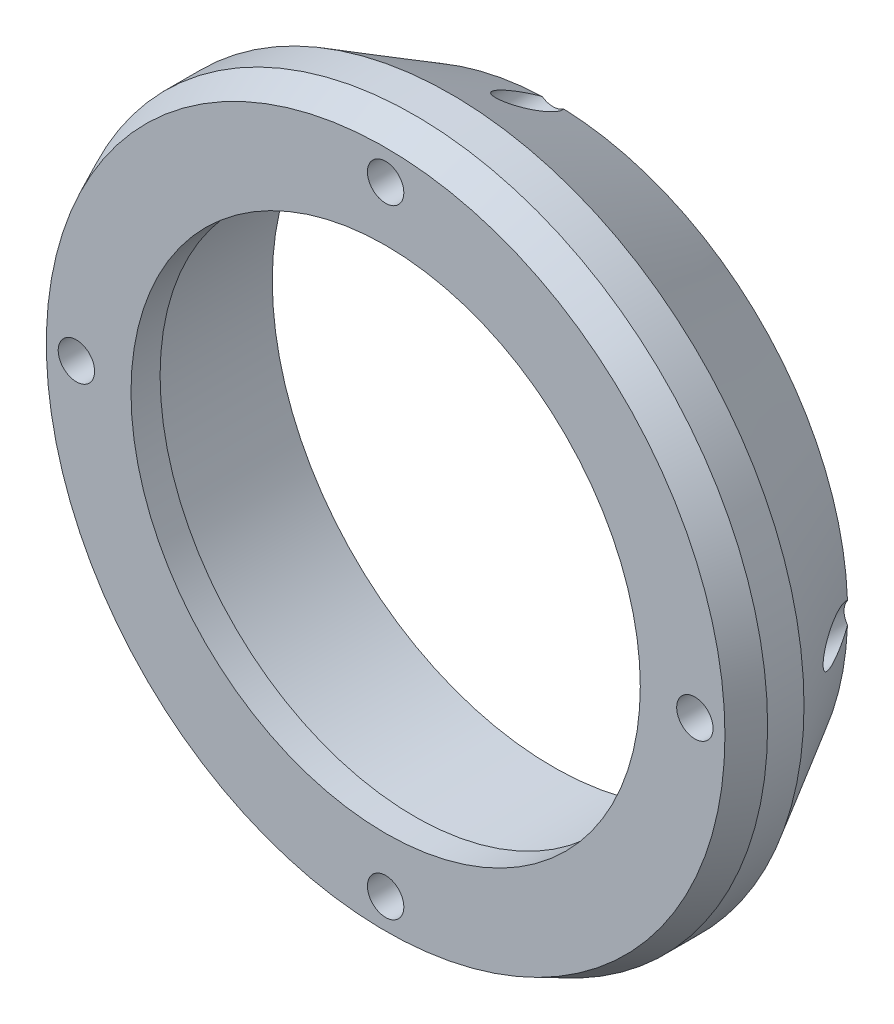
SolidWorks part; units mm, degrees
ref_plane "Front Plane" through (0, 0, 0) normal (0, 0, 1) x (1, 0, 0)
ref_plane "Top Plane" through (0, 0, 0) normal (0, 1, 0) x (1, 0, 0)
ref_plane "Right Plane" through (0, 0, 0) normal (1, 0, 0) x (0, 0, -1)
sketch "Sketch1" plane through (0, 0, 0) normal (0, 0, 1) x (1, 0, 0)
  circle A0 centre (0, 0) radius 44.45
  circle A1 centre (0, 0) radius 61.595
extrude "Extrude1" add sketch "Sketch1" along normal blind 29.21
sketch "Sketch2" plane through (0, 0, 0) normal (0, 0, -1) x (-1, 0, 0)
  circle A0 centre (0, 0) radius 49
extrude "Extrude2" cut sketch "Sketch2" against normal blind 24.13
sketch "Sketch3" plane through (0, 0, 29.21) normal (0, 0, 1) x (1, 0, 0)
  line L0 (0, 61.595) -> (0, 53.975) construction
  circle A0 centre (0, 0) radius 61.595 construction
chamfer "Chamfer2" distance 10.16 distance2 17.78 1 edges at (61.595, 0, 0)
hole_wizard "1/4 (0.25) Diameter Hole1" positions "Sketch5" profile "Sketch4" hole size "1/4" standard "Ansi Inch" end condition through all
sketch "Sketch5" plane through (0, 0, 29.21) normal (0, 0, 1) x (1, 0, 0)
  point P1 (0, 53.975)
sketch "Sketch4" plane through (0, 53.975, 29.21) normal (1, 0, 0) x (0, -1, 0)
  line L0 (0, 0) -> (0, 29.21)
  line L1 (0, 29.21) -> (3.175, 29.21)
  line L2 (3.175, 29.21) -> (3.175, 0)
  line L5 (3.175, 0) -> (0, 0)
  line L11 (0, -6.35) -> (0, 107.95) construction
  dimension "Thru Hole Dia." = 6.35
  dimension "Thru Hole Depth" = 29.21
pattern_circular "CirPattern1" count 4 over 360 about axis through (0, 0, 0) along (0, 0, 1) of "1/4 (0.25) Diameter Hole1"
sketch "Sketch6" plane through (0, 0, 29.21) normal (0, 0, 1) x (1, 0, 0)
  point P0 (53.975, 0)
  point P1 (-53.975, 0)
  point P3 (0, -53.975)
chamfer "Chamfer1" distance 5.08 angle 25 1 edges at (61.595, 0, 29.21)
